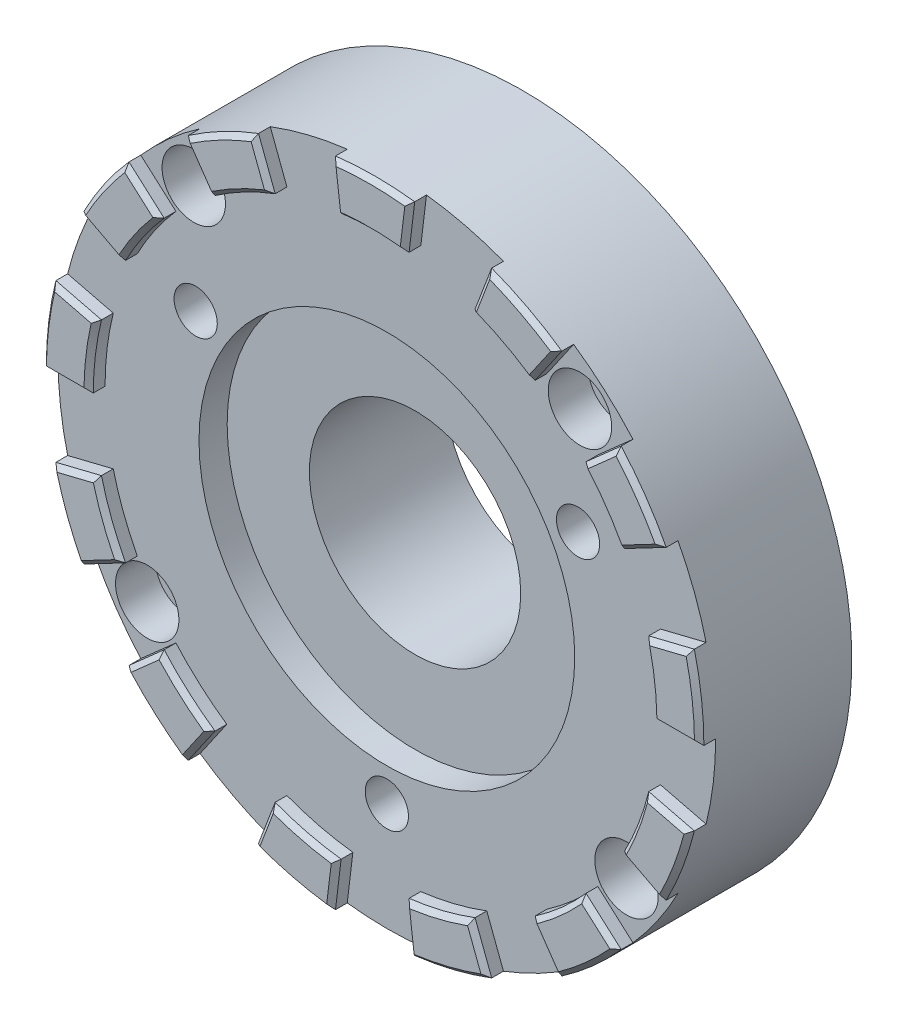
SolidWorks part; units mm, degrees
ref_plane "前视基准面" through (0, 0, 0) normal (0, 0, 1) x (1, 0, 0)
ref_plane "上视基准面" through (0, 0, 0) normal (0, 1, 0) x (1, 0, 0)
ref_plane "右视基准面" through (0, 0, 0) normal (1, 0, 0) x (0, 0, -1)
sketch "草图1" plane through (0, 0, 0) normal (0, 0, 1) x (1, 0, 0)
  circle A0 centre (0, 0) radius 70
  dimension "D1" = 140
extrude "凸台-拉伸1" add sketch "草图1" along normal blind 35
sketch "草图2" plane through (0, 0, 35) normal (0, 0, 1) x (1, 0, 0)
  line L0 (60, 0) -> (70, 0)
  line L1 (58.2565, 14.3589) -> (67.9659, 16.7521)
  line L2 (53.1274, 27.8834) -> (61.9819, 32.5306)
  line L3 (44.9106, 39.7874) -> (52.3958, 46.4186)
  line L4 (34.0839, 49.379) -> (39.7645, 57.6089)
  line L5 (21.2763, 56.101) -> (24.8223, 65.4511)
  line L6 (7.2322, 59.5625) -> (8.4376, 69.4896)
  line L7 (-7.2322, 59.5625) -> (-8.4376, 69.4896)
  line L8 (-21.2763, 56.101) -> (-24.8223, 65.4511)
  line L9 (-34.0839, 49.379) -> (-39.7645, 57.6089)
  line L10 (-44.9106, 39.7874) -> (-52.3958, 46.4186)
  line L11 (-53.1274, 27.8834) -> (-61.9819, 32.5306)
  line L12 (-58.2565, 14.3589) -> (-67.9659, 16.7521)
  line L13 (-60, 0) -> (-70, 0)
  line L14 (-58.2565, -14.3589) -> (-67.9659, -16.7521)
  line L15 (-53.1274, -27.8834) -> (-61.9819, -32.5306)
  line L16 (-44.9106, -39.7874) -> (-52.3958, -46.4186)
  line L17 (-34.0839, -49.379) -> (-39.7645, -57.6089)
  line L18 (-21.2763, -56.101) -> (-24.8223, -65.4511)
  line L19 (-7.2322, -59.5625) -> (-8.4376, -69.4896)
  line L20 (7.2322, -59.5625) -> (8.4376, -69.4896)
  line L21 (21.2763, -56.101) -> (24.8223, -65.4511)
  line L22 (34.0839, -49.379) -> (39.7645, -57.6089)
  line L23 (44.9106, -39.7874) -> (52.3958, -46.4186)
  line L24 (53.1274, -27.8834) -> (61.9819, -32.5306)
  line L25 (58.2565, -14.3589) -> (67.9659, -16.7521)
  arc A0 (53.1274, 27.8834) -> (44.9106, 39.7874) centre (0, 0) ccw
  circle A1 centre (0, 0) radius 70 construction
  arc A2 (61.9819, 32.5306) -> (52.3958, 46.4186) centre (0, 0) ccw
  arc A3 (39.7645, 57.6089) -> (24.8223, 65.4511) centre (0, 0) ccw
  arc A4 (34.0839, 49.379) -> (21.2763, 56.101) centre (0, 0) ccw
  arc A5 (8.4376, 69.4896) -> (-8.4376, 69.4896) centre (0, 0) ccw
  arc A6 (7.2322, 59.5625) -> (-7.2322, 59.5625) centre (0, 0) ccw
  arc A7 (-21.2763, 56.101) -> (-34.0839, 49.379) centre (0, 0) ccw
  arc A8 (-24.8223, 65.4511) -> (-39.7645, 57.6089) centre (0, 0) ccw
  arc A9 (-52.3958, 46.4186) -> (-61.9819, 32.5306) centre (0, 0) ccw
  arc A10 (-44.9106, 39.7874) -> (-53.1274, 27.8834) centre (0, 0) ccw
  arc A11 (-58.2565, 14.3589) -> (-60, 0) centre (0, 0) ccw
  arc A12 (-67.9659, 16.7521) -> (-70, 0) centre (0, 0) ccw
  arc A13 (-67.9659, -16.7521) -> (-61.9819, -32.5306) centre (0, 0) ccw
  arc A14 (-58.2565, -14.3589) -> (-53.1274, -27.8834) centre (0, 0) ccw
  arc A15 (-44.9106, -39.7874) -> (-34.0839, -49.379) centre (0, 0) ccw
  arc A16 (-52.3958, -46.4186) -> (-39.7645, -57.6089) centre (0, 0) ccw
  arc A17 (-21.2763, -56.101) -> (-7.2322, -59.5625) centre (0, 0) ccw
  arc A18 (-24.8223, -65.4511) -> (-8.4376, -69.4896) centre (0, 0) ccw
  arc A19 (7.2322, -59.5625) -> (21.2763, -56.101) centre (0, 0) ccw
  arc A20 (8.4376, -69.4896) -> (24.8223, -65.4511) centre (0, 0) ccw
  arc A21 (39.7645, -57.6089) -> (52.3958, -46.4186) centre (0, 0) ccw
  arc A22 (34.0839, -49.379) -> (44.9106, -39.7874) centre (0, 0) ccw
  arc A23 (53.1274, -27.8834) -> (58.2565, -14.3589) centre (0, 0) ccw
  arc A24 (61.9819, -32.5306) -> (67.9659, -16.7521) centre (0, 0) ccw
  arc A25 (70, 0) -> (67.9659, 16.7521) centre (0, 0) ccw
  arc A26 (60, 0) -> (58.2565, 14.3589) centre (0, 0) ccw
  dimension "D1" = 120
extrude "凸台-拉伸2" add sketch "草图2" along normal blind 3.5
chamfer "倒角1" distance 1 angle 45 52 edges at (63.1112, 15.5555, 38.5) (69.4896, 8.4376, 38.5) (65, 0, 38.5) (59.5625, 7.2322, 38.5) (63.1112, -15.5555, 38.5) (65.4511, -24.8223, 38.5) (57.5546, -30.207, 38.5) (56.101, -21.2763, 38.5) (48.6532, -43.103, 38.5) (46.4186, -52.3958, 38.5) (36.9242, -53.494, 38.5) (39.7874, -44.9106, 38.5) (23.0493, -60.7761, 38.5) (16.7521, -67.9659, 38.5) (7.8349, -64.5261, 38.5) (14.3589, -58.2565, 38.5) (-7.8349, -64.5261, 38.5) (-16.7521, -67.9659, 38.5) (-23.0493, -60.7761, 38.5) (-14.3589, -58.2565, 38.5) (-36.9242, -53.494, 38.5) (-46.4186, -52.3958, 38.5) (-48.6532, -43.103, 38.5) (-39.7874, -44.9106, 38.5) (-57.5546, -30.207, 38.5) (-65.4511, -24.8223, 38.5) (-63.1112, -15.5555, 38.5) (-56.101, -21.2763, 38.5) (-65, 0, 38.5) (-69.4896, 8.4376, 38.5) (-63.1112, 15.5555, 38.5) (-59.5625, 7.2322, 38.5) (-48.6532, 43.103, 38.5) (-49.379, 34.0839, 38.5) (-57.5546, 30.207, 38.5) (-57.6089, 39.7645, 38.5) (-23.0493, 60.7761, 38.5) (-27.8834, 53.1274, 38.5) (-36.9242, 53.494, 38.5) (-32.5306, 61.9819, 38.5) (7.8349, 64.5261, 38.5) (0, 60, 38.5) (-7.8349, 64.5261, 38.5) (0, 70, 38.5) (36.9242, 53.494, 38.5) (27.8834, 53.1274, 38.5) (23.0493, 60.7761, 38.5) (32.5306, 61.9819, 38.5) (57.5546, 30.207, 38.5) (49.379, 34.0839, 38.5) (48.6532, 43.103, 38.5) (57.6089, 39.7645, 38.5)
sketch "草图3" plane through (0, 0, 35) normal (0, 0, 1) x (1, 0, 0)
  circle A0 centre (0, 0) radius 40
  dimension "D1" = 80
extrude "切除-拉伸1" cut sketch "草图3" against normal blind 6
sketch "草图5" plane through (0, 0, 0) normal (0, 0, -1) x (-1, 0, 0)
  circle A0 centre (-40.7032, 23.5) radius 4.6
  circle A1 centre (-40.7032, 23.5) radius 4.6 construction
  circle A2 centre (40.7032, 23.5) radius 4.6
  circle A3 centre (0, -47) radius 4.6
  dimension "D1" = 9.2
  dimension "D2" = 3
extrude "切除-拉伸2" cut sketch "草图5" against normal blind 49
sketch "草图6" plane through (0, 0, 0) normal (0, 0, -1) x (-1, 0, 0)
  circle A0 centre (0, 0) radius 70 construction
  circle A1 centre (0, 0) radius 70
  circle A3 centre (0, 0) radius 55
  dimension "D1" = 15
extrude "切除-拉伸3" cut sketch "草图6" against normal blind 6
sketch "草图7" plane through (0, 0, 35) normal (0, 0, 1) x (1, 0, 0)
  line L0 (69.4896, -8.4376) -> (0, 0) construction
  arc A1 (67.9659, -16.7521) -> (70, 0) centre (0, 0) ccw construction
  circle A2 centre (51.025, -35.22) radius 6.75
  circle A6 centre (-51.025, -35.22) radius 6.75
  circle A9 centre (-41.1136, 46.4077) radius 6.75
  circle A12 centre (41.1136, 46.4077) radius 6.75
  dimension "D1" = 13.5
  dimension "D2" = 62
extrude "切除-拉伸4" cut sketch "草图7" against normal blind 8.5
sketch "草图8" plane through (0, 0, 26.5) normal (0, 0, 1) x (1, 0, 0)
  circle A0 centre (41.1136, 46.4077) radius 4
  circle A1 centre (51.025, -35.22) radius 4
  circle A2 centre (-51.025, -35.22) radius 4
  circle A3 centre (-41.1136, 46.4077) radius 4
  dimension "D1" = 8
  dimension "D2" = 8
  dimension "D3" = 8
  dimension "D4" = 8
extrude "切除-拉伸5" cut sketch "草图8" against normal blind 40.5
sketch "草图9" plane through (0, 0, 29) normal (0, 0, 1) x (1, 0, 0)
  circle A0 centre (0, 0) radius 22.5
  dimension "D1" = 45
extrude "切除-拉伸6" cut sketch "草图9" against normal blind 49.5
